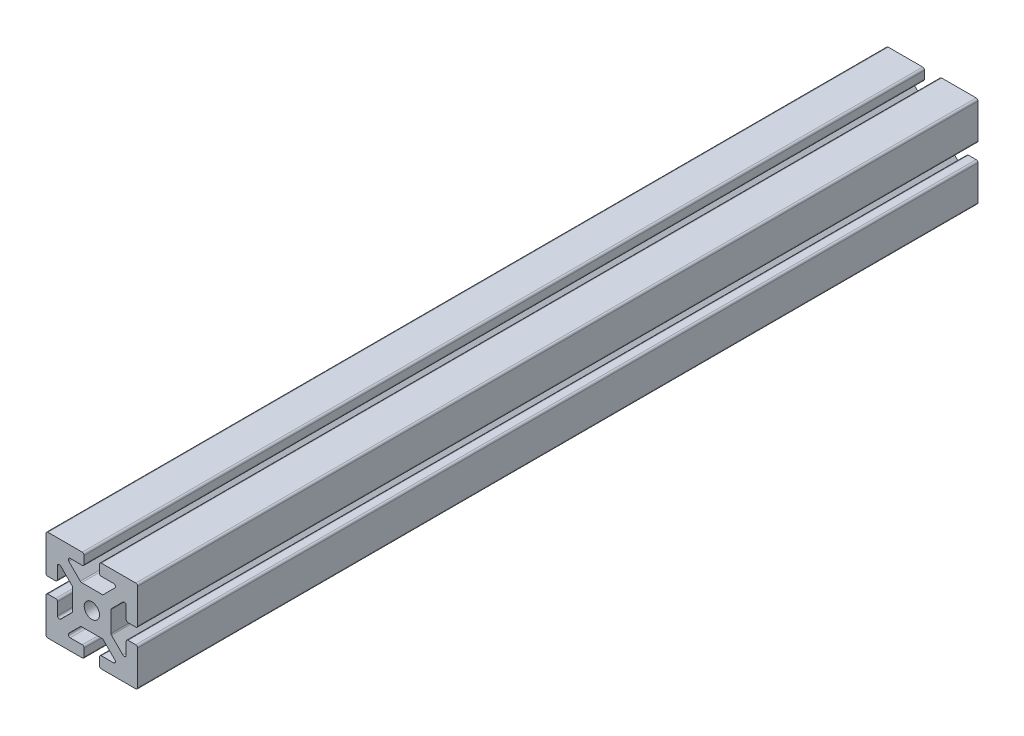
SolidWorks part; units mm, degrees
ref_plane "Front Plane" through (0, 0, 0) normal (0, 0, 1) x (1, 0, 0)
ref_plane "Top Plane" through (0, 0, 0) normal (0, 1, 0) x (1, 0, 0)
ref_plane "Right Plane" through (0, 0, 0) normal (1, 0, 0) x (0, 0, -1)
sketch "Sketch1" plane through (0, 0, 0) normal (0, 0, 1) x (1, 0, 0)
  line L0 (-5.75, 1) -> (-4.75, 1)
  line L5 (-1.3358, 2.5) -> (2.3964, 2.5)
  line L6 (-2.5, 1.3358) -> (-2.5, -1.3358)
  line L11 (-1.3358, -2.5) -> (1.3358, -2.5)
  line L12 (2.5, 1.3358) -> (2.5, -1.3358)
  line L17 (-5.75, -1) -> (-4.75, -1)
  line L18 (-1, 5.75) -> (-1, 4.75)
  line L19 (-2.8358, 4.5) -> (-1.25, 4.5)
  line L20 (0.25, 0) -> (3.445, 0) construction
  line L21 (3.445, 0) -> (-1, 0) construction
  line L22 (-4.5, 2.8358) -> (-4.5, 1.25)
  line L23 (-2.8358, -4.5) -> (-1.25, -4.5)
  line L24 (4.5, 2.8358) -> (4.5, 1.25)
  line L25 (1, 5.75) -> (1, 4.75)
  line L26 (-1, -4.75) -> (-1, -5.75)
  line L27 (-5.75, 6) -> (-1.25, 6)
  line L28 (-6, 5.75) -> (-6, 1.25)
  line L29 (-5.75, -6) -> (-1.25, -6)
  line L30 (6, 5.75) -> (6, 1.25)
  line L31 (4.75, 1) -> (5.75, 1)
  line L32 (1, -4.75) -> (1, -5.75)
  line L33 (4.75, -1) -> (5.75, -1)
  line L34 (0, 0.25) -> (0, 2.5) construction
  line L35 (0, 2.5) -> (0, -10.1662) construction
  line L36 (1.25, 6) -> (5.75, 6)
  line L37 (1.25, 4.5) -> (2.8358, 4.5)
  line L38 (4.5, -1.25) -> (4.5, -2.8358)
  line L39 (6, -1.25) -> (6, -5.75)
  line L40 (1.25, -4.5) -> (2.8358, -4.5)
  line L41 (1.25, -6) -> (5.75, -6)
  line L42 (-6, -1.25) -> (-6, -5.75)
  line L43 (-4.5, -1.25) -> (-4.5, -2.8358)
  line L44 (1.4393, 2.5) -> (3.0126, 4.0732)
  line L45 (2.5732, 2.5732) -> (4.5, 4.5) construction
  line L46 (4.0732, 3.0126) -> (2.5732, 1.5126)
  line L47 (4.0732, -3.0126) -> (2.5732, -1.5126)
  line L48 (1.5126, -2.5732) -> (3.0126, -4.0732)
  line L49 (-1.5126, -2.5732) -> (-3.0126, -4.0732)
  line L50 (-4.0732, -3.0126) -> (-2.5732, -1.5126)
  line L51 (-4.0732, 3.0126) -> (-2.5732, 1.5126)
  line L52 (-1.5126, 2.5732) -> (-3.0126, 4.0732)
  line L53 (-2.5, 0) -> (-2.9488, 0) construction
  circle A1 centre (0, 0) radius 1
  arc A2 (-3.0126, 4.0732) -> (-2.8358, 4.5) centre (-2.8358, 4.25) cw
  arc A3 (-1.5126, 2.5732) -> (-1.3358, 2.5) centre (-1.3358, 2.75) ccw
  arc A4 (-2.5732, 1.5126) -> (-2.5, 1.3358) centre (-2.75, 1.3358) cw
  arc A5 (-4.0732, 3.0126) -> (-4.5, 2.8358) centre (-4.25, 2.8358) ccw
  arc A6 (-2.5732, -1.5126) -> (-2.5, -1.3358) centre (-2.75, -1.3358) ccw
  arc A7 (-4.0732, -3.0126) -> (-4.5, -2.8358) centre (-4.25, -2.8358) cw
  arc A8 (-3.0126, -4.0732) -> (-2.8358, -4.5) centre (-2.8358, -4.25) ccw
  arc A9 (-1.5126, -2.5732) -> (-1.3358, -2.5) centre (-1.3358, -2.75) cw
  arc A10 (3.0126, -4.0732) -> (2.8358, -4.5) centre (2.8358, -4.25) cw
  arc A11 (1.5126, -2.5732) -> (1.3358, -2.5) centre (1.3358, -2.75) ccw
  arc A12 (2.5732, -1.5126) -> (2.5, -1.3358) centre (2.75, -1.3358) cw
  arc A13 (2.5732, 1.5126) -> (2.5, 1.3358) centre (2.75, 1.3358) ccw
  arc A14 (4.5, 2.8358) -> (4.0732, 3.0126) centre (4.25, 2.8358) ccw
  arc A15 (4.0732, -3.0126) -> (4.5, -2.8358) centre (4.25, -2.8358) ccw
  arc A16 (3.0126, 4.0732) -> (2.8358, 4.5) centre (2.8358, 4.25) ccw
  arc A17 (-4.75, -1) -> (-4.5, -1.25) centre (-4.75, -1.25) cw
  arc A18 (1, -4.75) -> (1.25, -4.5) centre (1.25, -4.75) cw
  arc A19 (4.75, 1) -> (4.5, 1.25) centre (4.75, 1.25) cw
  arc A20 (4.75, -1) -> (4.5, -1.25) centre (4.75, -1.25) ccw
  arc A21 (-4.75, 1) -> (-4.5, 1.25) centre (-4.75, 1.25) ccw
  arc A22 (1, 4.75) -> (1.25, 4.5) centre (1.25, 4.75) ccw
  arc A23 (-1, 4.75) -> (-1.25, 4.5) centre (-1.25, 4.75) cw
  arc A24 (-1, -4.75) -> (-1.25, -4.5) centre (-1.25, -4.75) ccw
  arc A25 (1.25, -6) -> (1, -5.75) centre (1.25, -5.75) cw
  arc A26 (1, 5.75) -> (1.25, 6) centre (1.25, 5.75) cw
  arc A27 (-1.25, -6) -> (-1, -5.75) centre (-1.25, -5.75) ccw
  arc A28 (-1, 5.75) -> (-1.25, 6) centre (-1.25, 5.75) ccw
  arc A29 (6, -1.25) -> (5.75, -1) centre (5.75, -1.25) ccw
  arc A30 (-5.75, -1) -> (-6, -1.25) centre (-5.75, -1.25) ccw
  arc A31 (0.25, 0) -> (0, 0.25) centre (0.25, 0.25) cw construction
  arc A32 (6, 1.25) -> (5.75, 1) centre (5.75, 1.25) cw
  arc A33 (-5.75, 1) -> (-6, 1.25) centre (-5.75, 1.25) cw
  arc A34 (5.75, 6) -> (6, 5.75) centre (5.75, 5.75) cw
  arc A35 (-6, -5.75) -> (-5.75, -6) centre (-5.75, -5.75) ccw
  arc A36 (-5.75, 6) -> (-6, 5.75) centre (-5.75, 5.75) ccw
  arc A37 (5.75, -6) -> (6, -5.75) centre (5.75, -5.75) ccw
  arc A38 (2.3964, 2.5) -> (2.5732, 2.5732) centre (2.3964, 2.75) ccw
  point P7 (-3.4393, 4.5)
  point P52 (-1.4393, 2.5)
  point P55 (-2.5, 1.4393)
  point P58 (-4.5, 3.4393)
  point P61 (-2.5, -1.4393)
  point P64 (-4.5, -3.4393)
  point P67 (-3.4393, -4.5)
  point P70 (-1.4393, -2.5)
  point P73 (3.4393, -4.5)
  point P76 (1.4393, -2.5)
  point P79 (2.5, -1.4393)
  point P82 (2.5, 1.4393)
  point P85 (4.5, 3.4393)
  point P88 (4.5, -3.4393)
  point P91 (3.4393, 4.5)
  point P94 (-4.5, -1)
  point P97 (1, -4.5)
  point P102 (4.5, -1)
  point P107 (1, 4.5)
  point P114 (1, -6)
  point P117 (1, 6)
  point P124 (6, -1)
  point P127 (-6, -1)
  dimension "D1" = 2
  dimension "D19" = 0.25
  dimension "D2" = 2.5
  dimension "D3" = 2.5
  dimension "D4" = 2.5
  dimension "D5" = 2
  dimension "D6" = 2
  dimension "D7" = 2
  dimension "D8" = 2
  dimension "D9" = 2
  dimension "D10" = 2
  dimension "D11" = 1.5
  dimension "D12" = 1.5
  dimension "D13" = 1.5
  dimension "D14" = 1.5
  dimension "D15" = 1
  dimension "D16" = 1
  dimension "D17" = 1.5
  dimension "D18" = 0.75
extrude "Boss-Extrude1" add sketch "Sketch1" along normal mid plane 110
